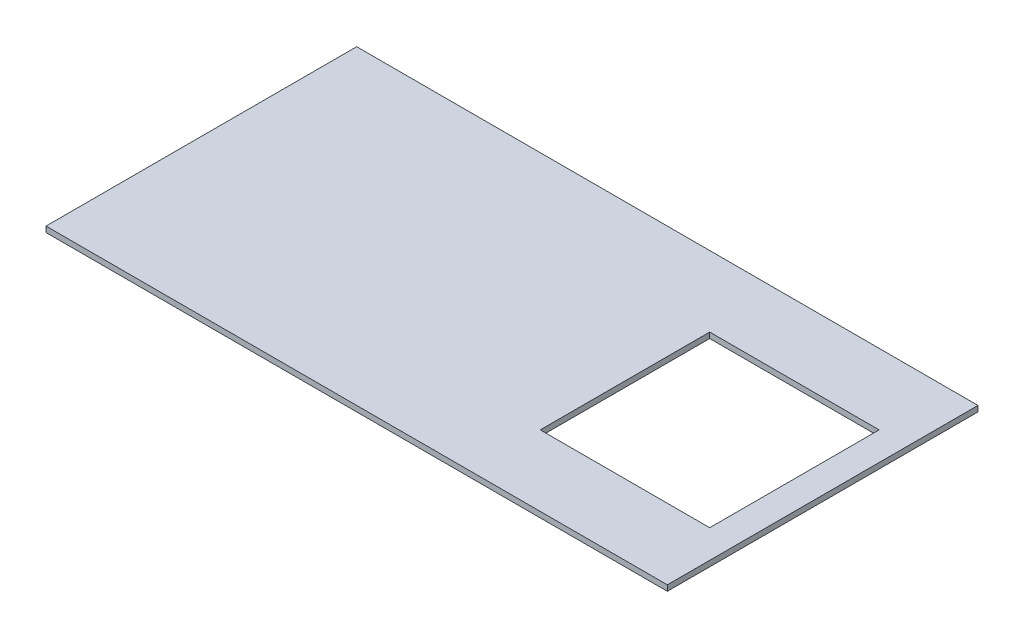
SolidWorks part; units mm, degrees
ref_plane "Front Plane" through (0, 0, 0) normal (0, 0, 1) x (1, 0, 0)
ref_plane "Top Plane" through (0, 0, 0) normal (0, 1, 0) x (1, 0, 0)
ref_plane "Right Plane" through (0, 0, 0) normal (1, 0, 0) x (0, 0, -1)
sketch "Sketch1" plane through (0, 0, 0) normal (0, 1, 0) x (1, 0, 0)
  line L1 (0, 0) -> (2200, 0)
  line L2 (0, 0) -> (0, 1100)
  line L3 (0, 1100) -> (2200, 1100)
  line L4 (2200, 0) -> (2200, 1100)
  dimension "D1" = 2200
  dimension "D2" = 1100
extrude "Extrude1" add sketch "Sketch1" along normal blind 20
sketch "Sketch2" plane through (0, 20, 0) normal (0, 1, 0) x (-1, 0, 0)
  line L0 (-2200, -1100) -> (0, -1100) construction
  line L1 (-1500, -850) -> (-2100, -850)
  line L2 (-1500, -850) -> (-1500, -250)
  line L3 (-1500, -250) -> (-2100, -250)
  line L4 (-2100, -850) -> (-2100, -250)
  line L6 (-2200, 0) -> (-2200, -1100) construction
  dimension "D1" = 600
  dimension "D2" = 600
  dimension "D3" = 250
  dimension "D4" = 100
extrude "Cut-Extrude1" cut sketch "Sketch2" against normal through all
